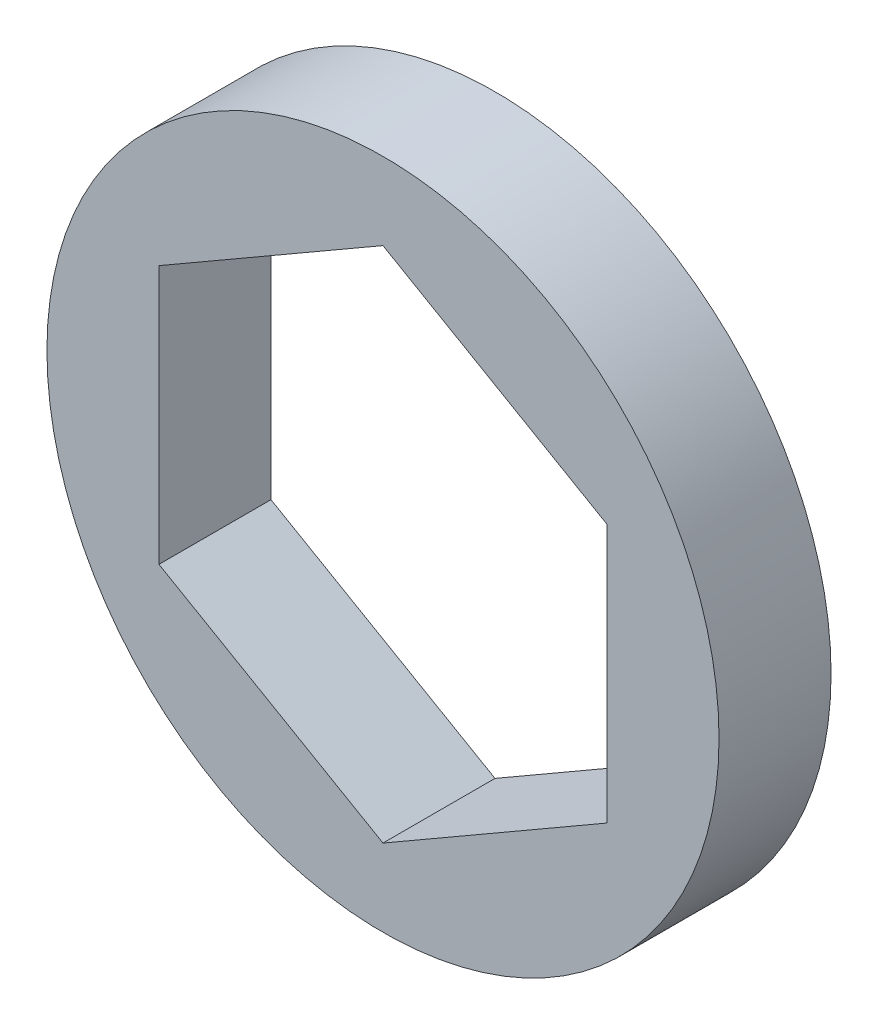
SolidWorks part; units mm, degrees
ref_plane "Front Plane" through (0, 0, 0) normal (0, 0, 1) x (1, 0, 0)
ref_plane "Top Plane" through (0, 0, 0) normal (0, 1, 0) x (1, 0, 0)
ref_plane "Right Plane" through (0, 0, 0) normal (1, 0, 0) x (0, 0, -1)
sketch "Sketch2" plane through (0, 0, 0) normal (0, 0, 1) x (1, 0, 0)
  line L1 (0, 7.3323) -> (-6.35, 3.6662)
  line L2 (-6.35, 3.6662) -> (-6.35, -3.6662)
  line L3 (-6.35, -3.6662) -> (0, -7.3323)
  line L4 (0, -7.3323) -> (6.35, -3.6662)
  line L5 (6.35, -3.6662) -> (6.35, 3.6662)
  line L6 (6.35, 3.6662) -> (0, 7.3323)
  circle A0 centre (0, 0) radius 6.35 construction
  circle A1 centre (0, 0) radius 9.525
  dimension "D1" = 19.05
  dimension ".5" = 12.7
extrude "Boss-Extrude1" add sketch "Sketch2" along normal blind 3.175 contours A1
